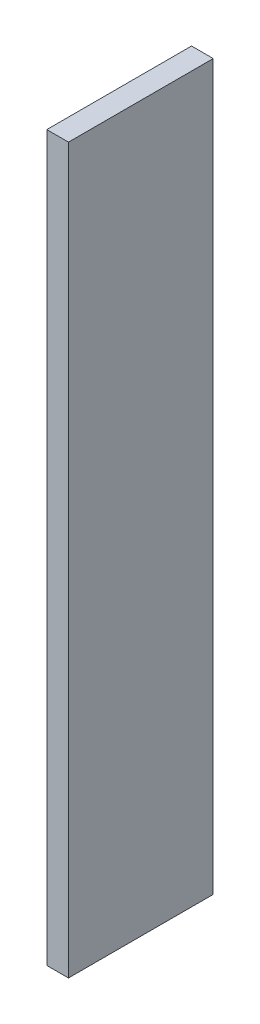
SolidWorks part; units mm, degrees
ref_plane "Front Plane" through (0, 0, 0) normal (0, 0, 1) x (1, 0, 0)
ref_plane "Top Plane" through (0, 0, 0) normal (0, 1, 0) x (1, 0, 0)
ref_plane "Right Plane" through (0, 0, 0) normal (1, 0, 0) x (0, 0, -1)
sketch "Sketch1" plane through (0, 0, 0) normal (1, 0, 0) x (0, 0, -1)
  line L1 (-10, -50) -> (10, -50)
  line L2 (-10, -50) -> (-10, 50)
  line L3 (-10, 50) -> (10, 50)
  line L4 (10, -50) -> (10, 50)
  line L5 (-10, -50) -> (10, 50) construction
  line L6 (-10, 50) -> (10, -50) construction
  point P0 (0, 0)
  dimension "D1" = 100
  dimension "D2" = 20
extrude "Boss-Extrude1" add sketch "Sketch1" along normal blind 3
